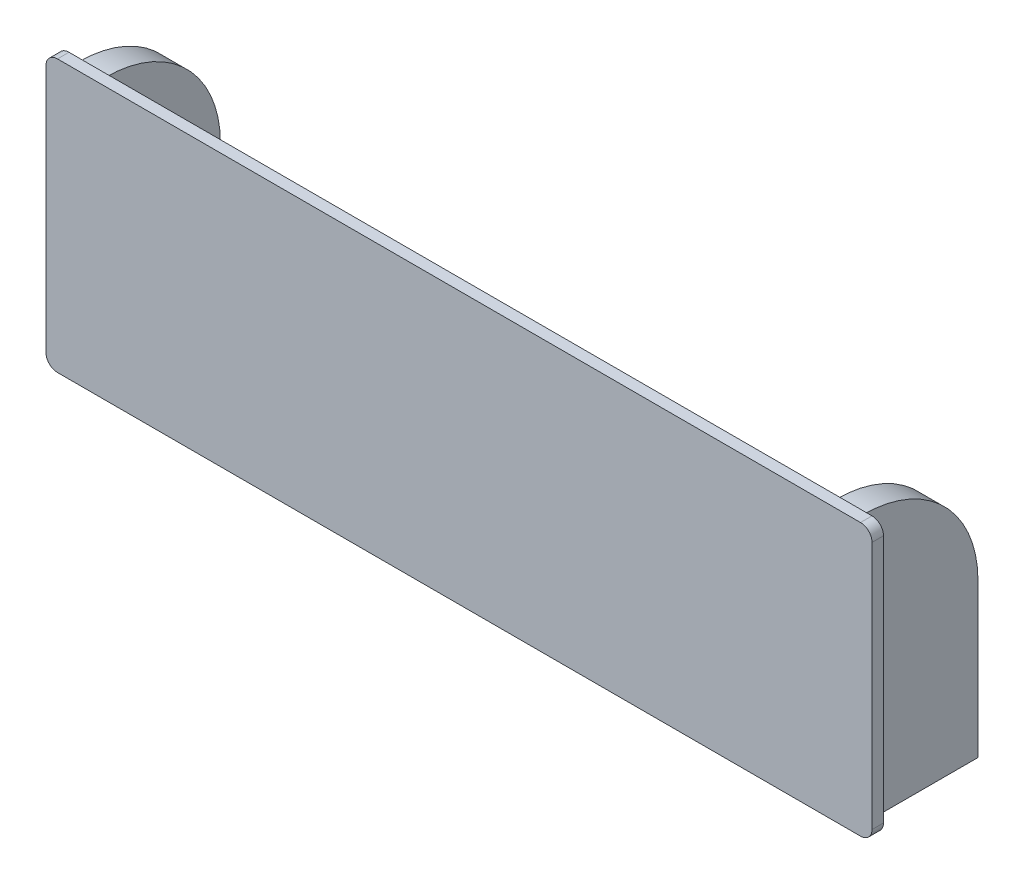
SolidWorks part; units mm, degrees
material "아크릴(내충격성)"
ref_plane "정면" through (0, 0, 0) normal (0, 0, 1) x (1, 0, 0)
ref_plane "윗면" through (0, 0, 0) normal (0, 1, 0) x (1, 0, 0)
ref_plane "우측면" through (0, 0, 0) normal (1, 0, 0) x (0, 0, -1)
sketch "스케치1" plane through (0, 0, 0) normal (0, 0, 1) x (1, 0, 0)
  line L1 (0, 0) -> (7, 0)
  line L2 (0, 0) -> (0, 70)
  line L3 (0, 70) -> (7, 70)
  line L4 (7, 0) -> (7, 70)
  line L5 (198, 0) -> (205, 0)
  line L6 (198, 0) -> (198, 70)
  line L7 (198, 70) -> (205, 70)
  line L8 (205, 0) -> (205, 70)
  dimension "D1" = 205
  dimension "D2" = 7
  dimension "D3" = 7
  dimension "D4" = 70
  dimension "D5" = 70
extrude "보스-돌출1" add sketch "스케치1" along normal blind 30.15
fillet "필렛1" radius 30 1 edges at (201.5, 70, 0)
fillet "필렛2" radius 30 1 edges at (3.5, 70, 0)
sketch "스케치2" plane through (0, 0, 30.15) normal (0, 0, 1) x (1, 0, 0)
  line L1 (210.45, 0) -> (-5.45, 0)
  line L2 (210.45, 0) -> (210.45, 71)
  line L3 (210.45, 71) -> (-5.45, 71)
  line L4 (-5.45, 0) -> (-5.45, 71)
  line L6 (205, 0) -> (205, 70) construction
  dimension "D1" = 215.9
  dimension "D2" = 71
  dimension "D3" = 0
  dimension "D4" = 5.45
extrude "보스-돌출2" add sketch "스케치2" along normal blind 3
fillet "필렛3" radius 3 4 edges at (-5.45, 0, 31.65) (210.45, 0, 31.65) (210.45, 71, 31.65) (-5.45, 71, 31.65)
